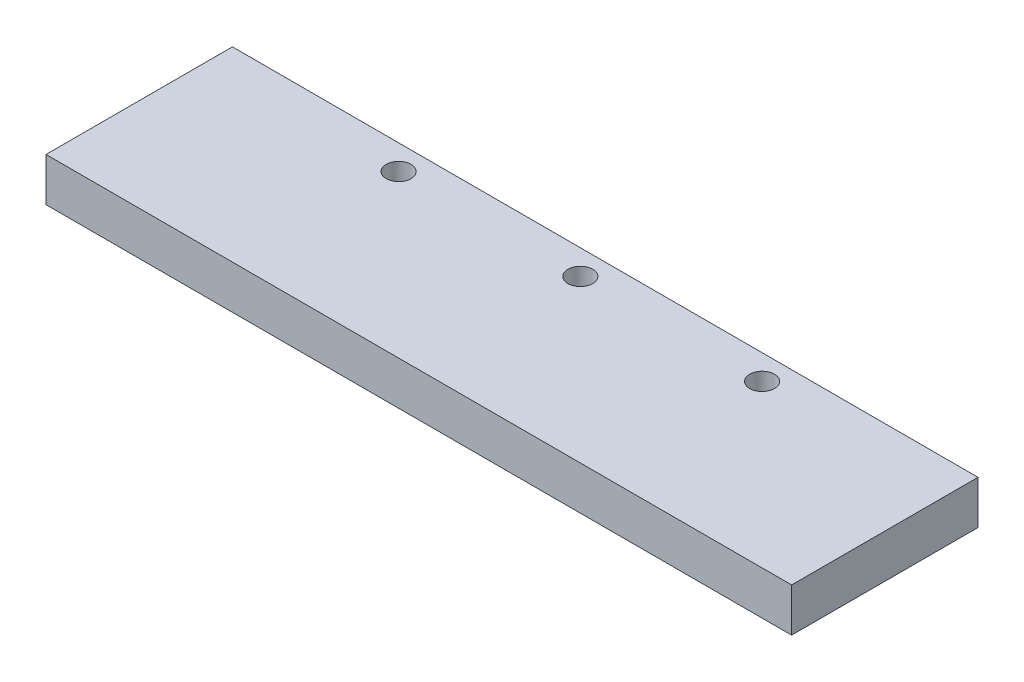
SolidWorks part; units mm, degrees
ref_plane "Front Plane" through (0, 0, 0) normal (0, 0, 1) x (1, 0, 0)
ref_plane "Top Plane" through (0, 0, 0) normal (0, 1, 0) x (1, 0, 0)
ref_plane "Right Plane" through (0, 0, 0) normal (1, 0, 0) x (0, 0, -1)
sketch "Sketch1" plane through (0, 0, 0) normal (0, 1, 0) x (1, 0, 0)
  line L1 (-102.5105, 65.1674) -> (17.4895, 65.1674)
  line L2 (-102.5105, 65.1674) -> (-102.5105, 35.1674)
  line L3 (-102.5105, 35.1674) -> (17.4895, 35.1674)
  line L4 (17.4895, 65.1674) -> (17.4895, 35.1674)
  dimension "D1" = 30
  dimension "D2" = 120
extrude "Boss-Extrude1" add sketch "Sketch1" along normal blind 7 contours L2 L3 L4 L1
sketch "Sketch2" plane through (0, 0, 0) normal (0, -1, 0) x (1, 0, 0)
  line L0 (-102.5105, -65.1674) -> (-102.5105, -35.1674) construction
  line L1 (-102.5105, -65.1674) -> (17.4895, -65.1674) construction
  line L3 (17.4895, -65.1674) -> (17.4895, -35.1674) construction
  circle A0 centre (-71.7605, -61.1674) radius 2
  circle A1 centre (-42.5105, -61.1674) radius 2
  circle A2 centre (-13.2605, -61.1674) radius 2
  point P12 (-143.8125, -15.9217)
  dimension "D1" = 30.75
  dimension "D5" = 29.25
  dimension "D7" = 30.75
  dimension "D2" = 4
  dimension "D3" = 29.25
  dimension "D4" = 4
  dimension "D6" = 4
extrude "Cut-Extrude1" cut sketch "Sketch2" against normal blind 10
